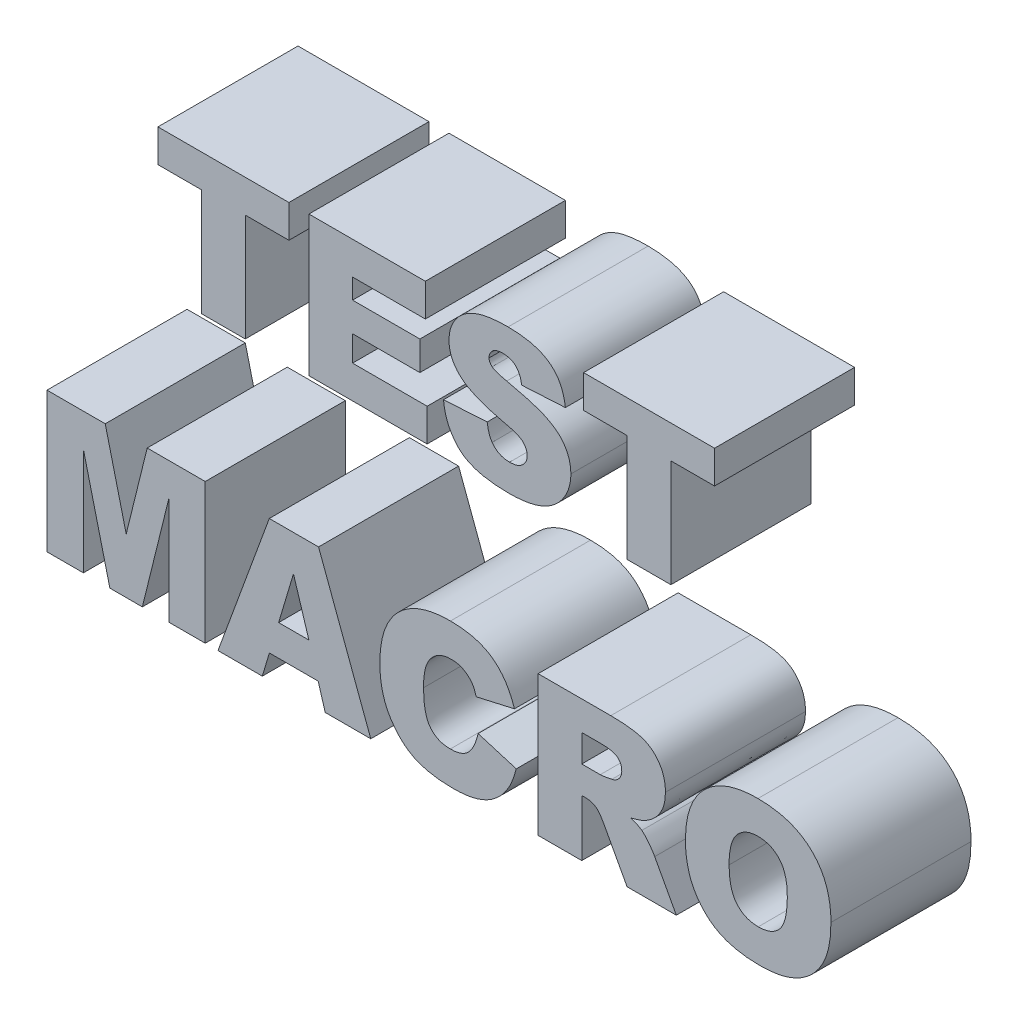
SolidWorks part; units mm, degrees
ref_plane "Plan de face" through (0, 0, 0) normal (0, 0, 1) x (1, 0, 0)
ref_plane "Plan de dessus" through (0, 0, 0) normal (0, 1, 0) x (1, 0, 0)
ref_plane "Plan de droite" through (0, 0, 0) normal (1, 0, 0) x (0, 0, -1)
sketch "Esquisse1" plane through (0, 0, 0) normal (0, 0, 1) x (1, 0, 0)
  line L0 (-123.8505, 0) -> (123.8505, 0) construction
  text T0 "TEST\r\nMACRO" font "Arial Black" height 20
  point P1 (-110.9479, 0)
  point P2 (123.8505, 0)
extrude "Boss.-Extru.1" add sketch "Esquisse1" along normal blind 20
